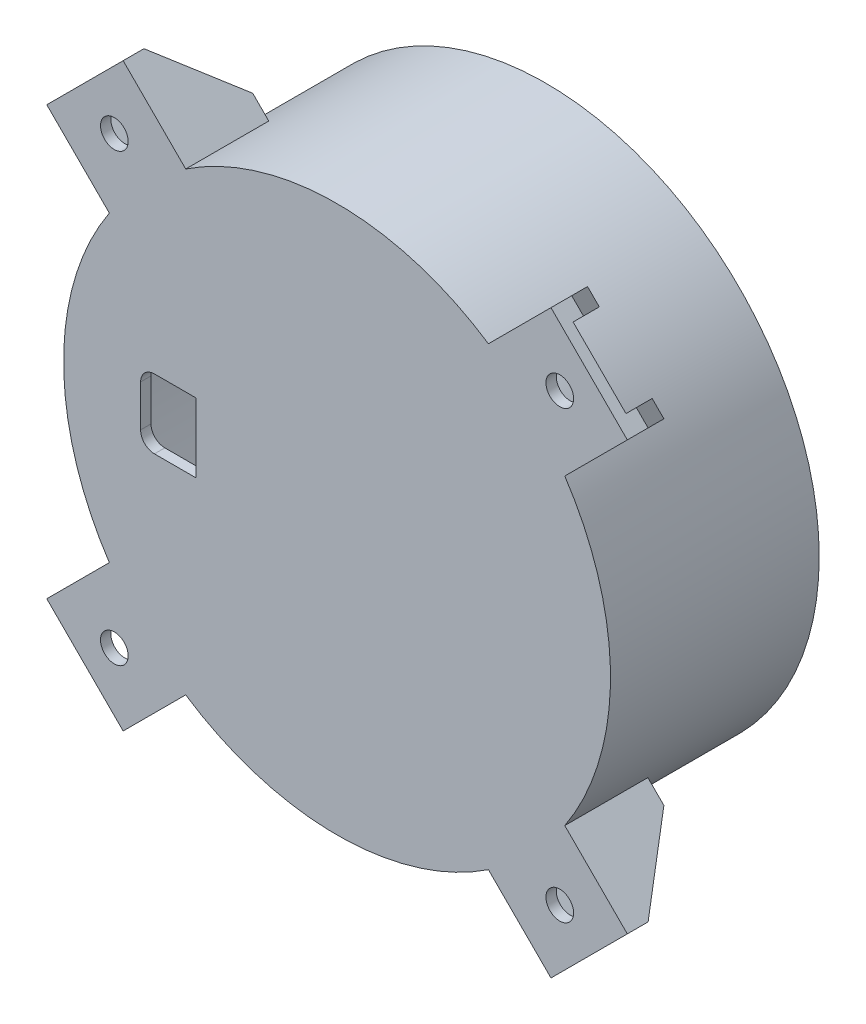
SolidWorks part; units mm, degrees
ref_plane "Front Plane" through (0, 0, 0) normal (0, 0, 1) x (1, 0, 0)
ref_plane "Top Plane" through (0, 0, 0) normal (0, 1, 0) x (1, 0, 0)
ref_plane "Right Plane" through (0, 0, 0) normal (1, 0, 0) x (0, 0, -1)
sketch "Sketch1" plane through (0, 0, 0) normal (0, 0, 1) x (1, 0, 0)
  circle A0 centre (-9.62, 10) radius 39.5
  dimension "D1" = 79
extrude "Boss-Extrude1" add sketch "Sketch1" along normal offset from surface (30.15 mm away) 2.4 contours A0
sketch "Sketch3" plane through (0, 0, 0) normal (0, 0, -1) x (-1, 0, 0)
  line L0 (-20, 20) -> (20, 20) construction
  line L1 (21, 20.5) -> (-21, 20.5)
  line L2 (21, 20.5) -> (21, -0.5)
  line L3 (21, -0.5) -> (-21, -0.5)
  line L4 (-21, 20.5) -> (-21, -0.5)
  line L5 (20, 20) -> (20, 0) construction
  line L6 (-20, 20) -> (-20, 0) construction
  line L7 (-20, 0) -> (20, 0) construction
  dimension "D1" = 0.5
  dimension "D2" = 1
  dimension "D3" = 1
  dimension "D4" = 0.5
extrude "Cut-Extrude1" cut sketch "Sketch3" against normal offset from surface (28.65 mm away) 1.5 up to face at (-49.12, 10, 30.15)
sketch "Sketch4" plane through (0, 0, 0) normal (0, 0, -1) x (-1, 0, 0)
  line L0 (-21, -0.5) -> (21, -0.5) construction
  line L1 (30, -1.8) -> (-25.5534, -1.8)
  line L2 (30, -1.8) -> (30, 21.8)
  line L3 (30, 21.8) -> (-25.5534, 21.8)
  line L5 (21, 20.5) -> (-21, 20.5) construction
  line L7 (27.5, 14.0271) -> (27.5, 5.9729) construction
  circle A2 centre (9.62, 10) radius 37.1
  arc A3 (-25.5534, -1.8) -> (-25.5534, 21.8) centre (9.62, 10) ccw
  dimension "D2" = 1.3
  dimension "D3" = 1.3
  dimension "D4" = 2.5
  dimension "D1" = 2.4
extrude "Cut-Extrude2" cut sketch "Sketch4" against normal offset from surface (28.65 mm away) 1.5 up to face at (-49.12, 10, 30.15)
sketch "Sketch5" plane through (0, 0, 0) normal (0, 0, -1) x (-1, 0, 0)
  line L0 (30, 21.8) -> (30, -1.8) construction
  line L1 (30, 7) -> (22.8134, 7)
  line L2 (30, 7) -> (30, 13)
  line L3 (30, 13) -> (22.8134, 13)
  line L4 (21, 7) -> (21, 13)
  line L5 (21, -0.5) -> (21, 20.5) construction
  line L6 (25, 6.46) -> (25, 7) construction
  line L7 (25, 13.54) -> (25, 13) construction
  line L8 (22.8134, 7) -> (21, 6)
  line L9 (21, 6) -> (21, 7)
  line L10 (22.8134, 13) -> (21, 14)
  line L11 (21, 14) -> (21, 13)
  circle A0 centre (25, 4.96) radius 1.5
  circle A1 centre (25, 15.04) radius 1.5
  circle A2 centre (-25, 4.96) radius 1.5
  circle A3 centre (-25, 15.04) radius 1.5
  dimension "D1" = 3
  dimension "D2" = 6
  dimension "D3" = 0.54
  dimension "D4" = 1
extrude "Cut-Extrude3" cut sketch "Sketch5" against normal offset from surface (28.65 mm away) 1.5 up to face at (-49.12, 10, 30.15)
sketch "Sketch8" plane through (0, 0, 28.65) normal (0, 0, -1) x (-1, 0, 0)
  line L1 (30, 15) -> (38, 15)
  line L2 (30, 15) -> (30, 5)
  line L3 (30, 5) -> (38, 5)
  line L4 (38, 15) -> (38, 5)
  line L6 (30, 21.8) -> (30, 13) construction
  line L7 (33.9077, 7) -> (33.9077, 5) construction
  line L8 (22.8134, 7) -> (30, 7) construction
  line L9 (33.9077, 13) -> (33.9077, 15) construction
  line L10 (30, 13) -> (22.8134, 13) construction
  dimension "D1" = 10
  dimension "D2" = 8
extrude "Cut-Extrude5" cut sketch "Sketch8" against normal through all
fillet "Fillet1" radius 3 2 edges at (-30, 21.8, 14.325) (-30, -1.8, 14.325)
fillet "Fillet3" radius 6 2 edges at (25.5534, 21.8, 14.325) (25.5534, -1.8, 14.325)
fillet "Fillet2" radius 2 8 edges at (-38, 5, 29.4) (-38, 15, 29.4) (-30, 7, 14.325) (-30, 13, 14.325) (-22.8134, 13, 14.325) (-22.8134, 7, 14.325) (-21, 14, 14.325) (-21, 6, 14.325)
sketch "Sketch12" plane through (0, 0, 30.15) normal (0, 0, 1) x (1, 0, 0)
  line L0 (29.88, 10) -> (-9.62, 10) construction
  line L1 (-9.62, 10) -> (18.3107, -17.9307) construction
  line L2 (23.8262, -12.4153) -> (12.7953, -23.4462) construction
  line L4 (22.9154, -11.5046) -> (32.3114, -20.9006)
  line L5 (11.8846, -22.5354) -> (21.2806, -31.9314)
  line L6 (32.3114, -20.9006) -> (21.2806, -31.9314)
  line L7 (18.3107, -17.9307) -> (26.796, -26.416) construction
  circle A0 centre (-9.62, 10) radius 39.5 construction
  circle A2 centre (22.5534, -22.1734) radius 2
  circle A5 centre (-9.62, 10) radius 39
  arc A6 (11.8846, -22.5354) -> (22.9154, -11.5046) centre (-9.62, 10) ccw
  point P10 (18.3107, -17.9307)
  dimension "D4" = 4
  dimension "D1" = 45
  dimension "D2" = 6
  dimension "D3" = 7.8
  dimension "D5" = 0.5
extrude "Boss-Extrude3" add sketch "Sketch12" against normal blind 12 separate body
sketch "Sketch13" plane through (-5.3254, -5.3254, 0) normal (-0.7071, -0.7071, 0) x (0, 0, 1)
  line L0 (18.15, -37.6266) -> (27.15, -37.6266)
  line L1 (18.15, -37.6266) -> (30.15, -37.6266) construction
  line L2 (27.15, -37.6266) -> (18.15, -28.1266)
  line L3 (18.15, -24.3386) -> (18.15, -37.6266) construction
  line L4 (18.15, -28.1266) -> (18.15, -37.6266)
  dimension "D1" = 9
  dimension "D2" = 9.5
extrude "Cut-Extrude6" cut sketch "Sketch13" against normal up to surface (15.6 mm away) up to face at (27.6134, -16.2026, 24.15)
sketch "Sketch14" plane through (0, 0, 18.15) normal (0, 0, -1) x (-1, 0, 0)
  line L0 (-14.2301, -21.4869) -> (-22.9776, -30.2344)
  line L1 (-32.3114, -20.9006) -> (-21.2806, -31.9314) construction
  line L2 (-22.9776, -30.2344) -> (-30.6144, -22.5976)
  line L3 (-30.6144, -22.5976) -> (-21.8669, -13.8501)
  line L4 (-32.3114, -20.9006) -> (-22.9154, -11.5046) construction
  line L5 (-11.8846, -22.5354) -> (-21.2806, -31.9314) construction
  circle A2 centre (9.62, 10) radius 39.5
  arc A3 (-21.8669, -13.8501) -> (-14.2301, -21.4869) centre (9.62, 10) ccw
  dimension "D2" = 2.4
  dimension "D3" = 2.4
  dimension "D1" = 0
extrude "Cut-Extrude7" cut sketch "Sketch14" against normal offset from surface (10.5 mm away) 1.5 up to face at (-34.8047, 10, 30.15)
pattern_circular "CirPattern19" count 4 over 360 about axis through (-9.62, 10, 0) along (0, 0, 1) of bodies 110
combine bodies "Combine1" bodies to combine 106 110 114 115 116
equation "\"oneLayer\"= 1.2mm'MOARstruder"
